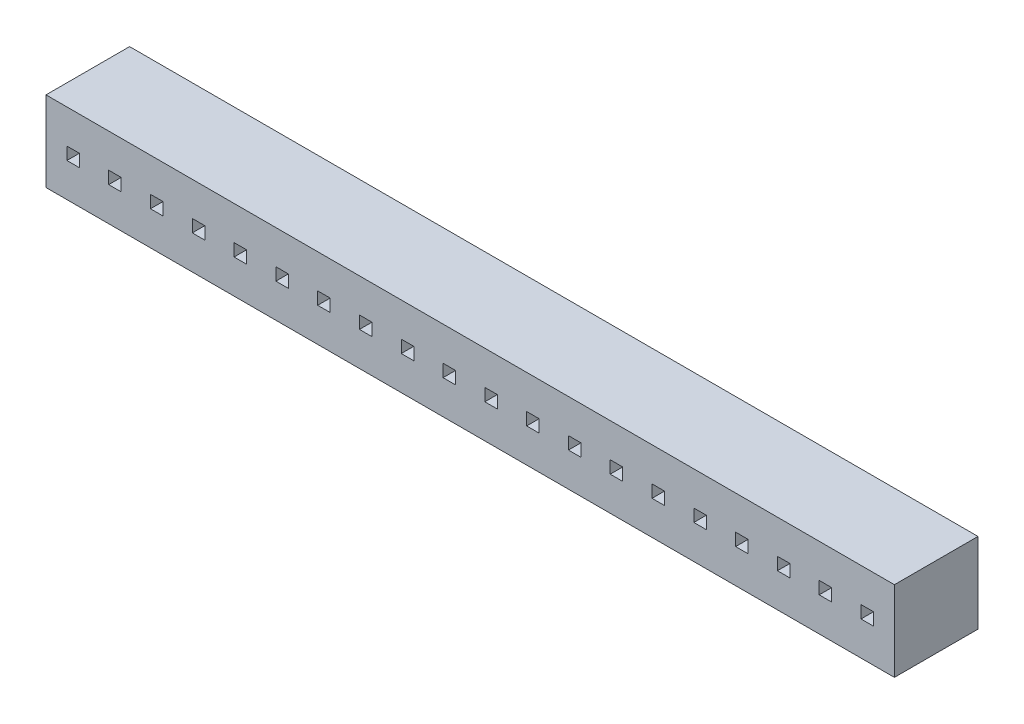
SolidWorks part; units mm, degrees
material "Liquid Crystal Polymer"
ref_plane "Front Plane" through (0, 0, 0) normal (0, 0, 1) x (1, 0, 0)
ref_plane "Top Plane" through (0, 0, 0) normal (0, 1, 0) x (1, 0, 0)
ref_plane "Right Plane" through (0, 0, 0) normal (1, 0, 0) x (0, 0, -1)
sketch "Sketch1" plane through (0, 0, 0) normal (0, 1, 0) x (1, 0, 0)
  line L1 (-12.89, -1.27) -> (12.89, -1.27)
  line L2 (-12.89, -1.27) -> (-12.89, 1.27)
  line L3 (-12.89, 1.27) -> (12.89, 1.27)
  line L4 (12.89, -1.27) -> (12.89, 1.27)
  line L5 (-12.89, -1.27) -> (12.89, 1.27) construction
  line L6 (-12.89, 1.27) -> (12.89, -1.27) construction
  point P0 (0, 0)
  dimension "D1" = 2.54
  dimension "D2" = 25.78
extrude "Boss-Extrude1" add sketch "Sketch1" along normal blind 2.44
sketch "Sketch2" plane through (0, 0, 1.27) normal (0, 0, 1) x (1, 0, 0)
  line L0 (-12.89, 1.22) -> (12.89, 1.22) construction
  line L1 (-12.89, 2.44) -> (-12.89, 0) construction
  line L2 (12.89, 2.44) -> (12.89, 0) construction
  line L3 (-10.605, 1.03) -> (-10.605, 1.41)
  line L4 (-12.255, 1.03) -> (-11.875, 1.03)
  line L5 (-12.255, 1.03) -> (-12.255, 1.41)
  line L6 (-12.255, 1.41) -> (-11.875, 1.41)
  line L7 (-11.875, 1.03) -> (-11.875, 1.41)
  line L8 (-12.255, 1.03) -> (-11.875, 1.41) construction
  line L9 (-12.255, 1.41) -> (-11.875, 1.03) construction
  line L10 (-10.985, 1.41) -> (-10.605, 1.41)
  line L11 (-10.985, 1.03) -> (-10.985, 1.41)
  line L12 (-10.985, 1.03) -> (-10.605, 1.41) construction
  line L13 (-10.985, 1.03) -> (-10.605, 1.03)
  line L14 (-10.985, 1.41) -> (-10.605, 1.03) construction
  line L15 (-9.335, 1.03) -> (-9.335, 1.41)
  line L16 (-9.715, 1.41) -> (-9.335, 1.41)
  line L17 (-9.715, 1.03) -> (-9.715, 1.41)
  line L18 (-9.715, 1.03) -> (-9.335, 1.41) construction
  line L19 (-9.715, 1.03) -> (-9.335, 1.03)
  line L20 (-9.715, 1.41) -> (-9.335, 1.03) construction
  line L21 (-8.065, 1.03) -> (-8.065, 1.41)
  line L22 (-8.445, 1.41) -> (-8.065, 1.41)
  line L23 (-8.445, 1.03) -> (-8.445, 1.41)
  line L24 (-8.445, 1.03) -> (-8.065, 1.41) construction
  line L25 (-8.445, 1.03) -> (-8.065, 1.03)
  line L26 (-8.445, 1.41) -> (-8.065, 1.03) construction
  line L27 (-6.795, 1.03) -> (-6.795, 1.41)
  line L28 (-7.175, 1.41) -> (-6.795, 1.41)
  line L29 (-7.175, 1.03) -> (-7.175, 1.41)
  line L30 (-7.175, 1.03) -> (-6.795, 1.41) construction
  line L31 (-7.175, 1.03) -> (-6.795, 1.03)
  line L32 (-7.175, 1.41) -> (-6.795, 1.03) construction
  line L33 (-5.525, 1.03) -> (-5.525, 1.41)
  line L34 (-5.905, 1.41) -> (-5.525, 1.41)
  line L35 (-5.905, 1.03) -> (-5.905, 1.41)
  line L36 (-5.905, 1.03) -> (-5.525, 1.41) construction
  line L37 (-5.905, 1.03) -> (-5.525, 1.03)
  line L38 (-5.905, 1.41) -> (-5.525, 1.03) construction
  line L39 (-4.255, 1.03) -> (-4.255, 1.41)
  line L40 (-4.635, 1.41) -> (-4.255, 1.41)
  line L41 (-4.635, 1.03) -> (-4.635, 1.41)
  line L42 (-4.635, 1.03) -> (-4.255, 1.41) construction
  line L43 (-4.635, 1.03) -> (-4.255, 1.03)
  line L44 (-4.635, 1.41) -> (-4.255, 1.03) construction
  line L45 (-2.985, 1.03) -> (-2.985, 1.41)
  line L46 (-3.365, 1.41) -> (-2.985, 1.41)
  line L47 (-3.365, 1.03) -> (-3.365, 1.41)
  line L48 (-3.365, 1.03) -> (-2.985, 1.41) construction
  line L49 (-3.365, 1.03) -> (-2.985, 1.03)
  line L50 (-3.365, 1.41) -> (-2.985, 1.03) construction
  line L51 (-1.715, 1.03) -> (-1.715, 1.41)
  line L52 (-2.095, 1.41) -> (-1.715, 1.41)
  line L53 (-2.095, 1.03) -> (-2.095, 1.41)
  line L54 (-2.095, 1.03) -> (-1.715, 1.41) construction
  line L55 (-2.095, 1.03) -> (-1.715, 1.03)
  line L56 (-2.095, 1.41) -> (-1.715, 1.03) construction
  line L57 (-0.445, 1.03) -> (-0.445, 1.41)
  line L58 (-0.825, 1.41) -> (-0.445, 1.41)
  line L59 (-0.825, 1.03) -> (-0.825, 1.41)
  line L60 (-0.825, 1.03) -> (-0.445, 1.41) construction
  line L61 (-0.825, 1.03) -> (-0.445, 1.03)
  line L62 (-0.825, 1.41) -> (-0.445, 1.03) construction
  line L63 (0.825, 1.03) -> (0.825, 1.41)
  line L64 (0.445, 1.41) -> (0.825, 1.41)
  line L65 (0.445, 1.03) -> (0.445, 1.41)
  line L66 (0.445, 1.03) -> (0.825, 1.41) construction
  line L67 (0.445, 1.03) -> (0.825, 1.03)
  line L68 (0.445, 1.41) -> (0.825, 1.03) construction
  line L69 (2.095, 1.03) -> (2.095, 1.41)
  line L70 (1.715, 1.41) -> (2.095, 1.41)
  line L71 (1.715, 1.03) -> (1.715, 1.41)
  line L72 (1.715, 1.03) -> (2.095, 1.41) construction
  line L73 (1.715, 1.03) -> (2.095, 1.03)
  line L74 (1.715, 1.41) -> (2.095, 1.03) construction
  line L75 (3.365, 1.03) -> (3.365, 1.41)
  line L76 (2.985, 1.41) -> (3.365, 1.41)
  line L77 (2.985, 1.03) -> (2.985, 1.41)
  line L78 (2.985, 1.03) -> (3.365, 1.41) construction
  line L79 (2.985, 1.03) -> (3.365, 1.03)
  line L80 (2.985, 1.41) -> (3.365, 1.03) construction
  line L81 (4.635, 1.03) -> (4.635, 1.41)
  line L82 (4.255, 1.41) -> (4.635, 1.41)
  line L83 (4.255, 1.03) -> (4.255, 1.41)
  line L84 (4.255, 1.03) -> (4.635, 1.41) construction
  line L85 (4.255, 1.03) -> (4.635, 1.03)
  line L86 (4.255, 1.41) -> (4.635, 1.03) construction
  line L87 (5.905, 1.03) -> (5.905, 1.41)
  line L88 (5.525, 1.41) -> (5.905, 1.41)
  line L89 (5.525, 1.03) -> (5.525, 1.41)
  line L90 (5.525, 1.03) -> (5.905, 1.41) construction
  line L91 (5.525, 1.03) -> (5.905, 1.03)
  line L92 (5.525, 1.41) -> (5.905, 1.03) construction
  line L93 (7.175, 1.03) -> (7.175, 1.41)
  line L94 (6.795, 1.41) -> (7.175, 1.41)
  line L95 (6.795, 1.03) -> (6.795, 1.41)
  line L96 (6.795, 1.03) -> (7.175, 1.41) construction
  line L97 (6.795, 1.03) -> (7.175, 1.03)
  line L98 (6.795, 1.41) -> (7.175, 1.03) construction
  line L99 (8.445, 1.03) -> (8.445, 1.41)
  line L100 (8.065, 1.41) -> (8.445, 1.41)
  line L101 (8.065, 1.03) -> (8.065, 1.41)
  line L102 (8.065, 1.03) -> (8.445, 1.41) construction
  line L103 (8.065, 1.03) -> (8.445, 1.03)
  line L104 (8.065, 1.41) -> (8.445, 1.03) construction
  line L105 (9.715, 1.03) -> (9.715, 1.41)
  line L106 (9.335, 1.41) -> (9.715, 1.41)
  line L107 (9.335, 1.03) -> (9.335, 1.41)
  line L108 (9.335, 1.03) -> (9.715, 1.41) construction
  line L109 (9.335, 1.03) -> (9.715, 1.03)
  line L110 (9.335, 1.41) -> (9.715, 1.03) construction
  line L111 (10.985, 1.03) -> (10.985, 1.41)
  line L112 (10.605, 1.41) -> (10.985, 1.41)
  line L113 (10.605, 1.03) -> (10.605, 1.41)
  line L114 (10.605, 1.03) -> (10.985, 1.41) construction
  line L115 (10.605, 1.03) -> (10.985, 1.03)
  line L116 (10.605, 1.41) -> (10.985, 1.03) construction
  line L117 (12.255, 1.03) -> (12.255, 1.41)
  line L118 (11.875, 1.41) -> (12.255, 1.41)
  line L119 (11.875, 1.03) -> (11.875, 1.41)
  line L120 (11.875, 1.03) -> (12.255, 1.41) construction
  line L121 (11.875, 1.03) -> (12.255, 1.03)
  line L122 (11.875, 1.41) -> (12.255, 1.03) construction
  point P6 (-12.065, 1.22)
  point P11 (-0.635, 1.22)
  point P12 (0, 0)
  point P89 (0, 0)
  dimension "D1" = 0.38
  dimension "D3" = 0.635
  dimension "D4" = 1.27
  dimension "D2" = 20
extrude "Cut-Extrude1" cut sketch "Sketch2" against normal up to next
equation "\"D3@Sketch2\"=1.27/2"
